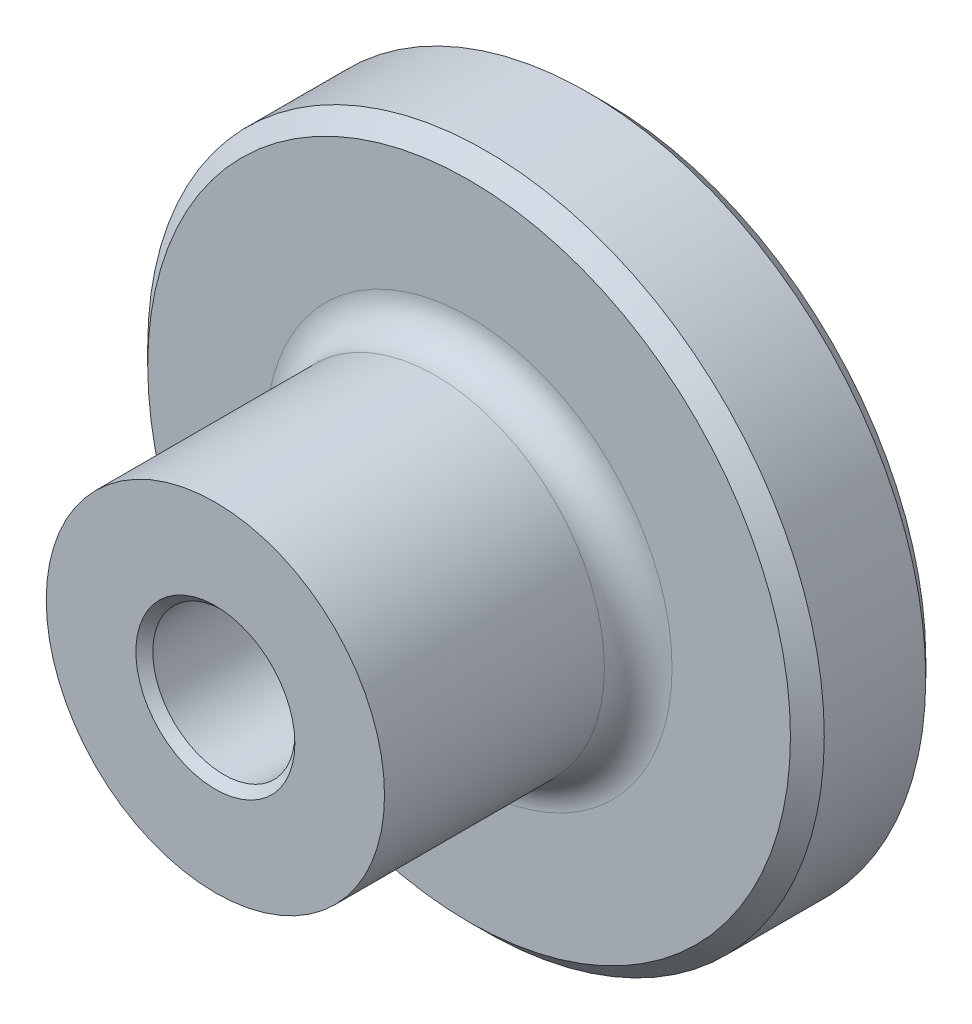
SolidWorks part; units mm, degrees
material "acero"
ref_plane "Alzado" through (0, 0, 0) normal (0, 0, 1) x (1, 0, 0)
ref_plane "Planta" through (0, 0, 0) normal (0, 1, 0) x (1, 0, 0)
ref_plane "Vista lateral" through (0, 0, 0) normal (1, 0, 0) x (0, 0, -1)
sketch "Croquis1" plane through (0, 0, 0) normal (0, 0, 1) x (1, 0, 0)
  circle A0 centre (0, 0) radius 10
  circle A1 centre (0, 0) radius 2.1
  dimension "D1" = 20
  dimension "D2" = 4.2
extrude "Saliente-Extruir1" add sketch "Croquis1" along normal blind 4
cosmetic thread "Rosca cosmética1" parameters "D2"=5
sketch "Croquis2" plane through (0, 0, 4) normal (0, 0, 1) x (1, 0, 0)
  circle A0 centre (0, 0) radius 5
  circle A1 centre (0, 0) radius 2.1 construction
  circle A2 centre (0, 0) radius 2.1
  dimension "D1" = 10
extrude "Saliente-Extruir2" add sketch "Croquis2" along normal blind 7.5
chamfer "Chaflán1" distance 0.5 angle 45 2 edges at (10, 0, 0) (10, 0, 4)
fillet "Redondeo1" radius 1 1 edges at (5, 0, 4)
chamfer "Chaflán2" distance 0.25 angle 45 1 edges at (2.1, 0, 11.5)
